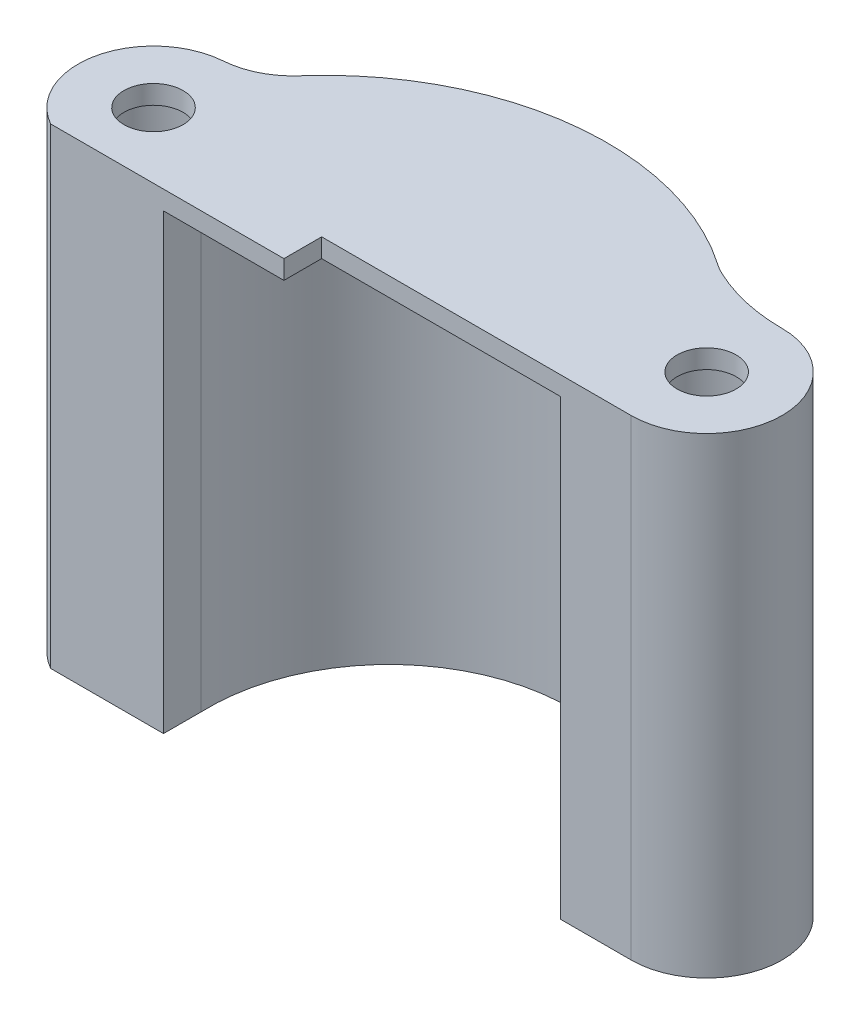
SolidWorks part; units mm, degrees
ref_plane "Front Plane" through (0, 0, 0) normal (0, 0, 1) x (1, 0, 0)
ref_plane "Top Plane" through (0, 0, 0) normal (0, 1, 0) x (1, 0, 0)
ref_plane "Right Plane" through (0, 0, 0) normal (1, 0, 0) x (0, 0, -1)
other "Bounding Box"
ref_plane "Default Plane" through (-8.9266, -12.7485, 0) normal (-0.1736, 0.9848, 0) x (0.9848, 0.1736, 0)
sketch "Sketch1" plane through (0, 0, 0) normal (0, 1, 0) x (1, 0, 0)
  line B0 (-13.6378, -15.7405) -> (-16.8128, -15.7405) construction
  line B1 (16.6091, -12.5655) -> (19.7841, -12.5655) construction
  arc B2 (-13.6378, -15.7405) -> (16.6091, -12.5655) centre (1.591, -15.1567) cw
  arc B3 (-16.8128, -15.7405) -> (19.7841, -12.5655) centre (1.6704, -16.283) cw
sketch_block_instance "Cover for wepon motor-1"
sketch_block "Cover for wepon motor" parameters "D3"=15.24, "D4"=18.4912, "D1"=3.175, "D2"=3.175
sketch "Sketch2" plane through (0, 0, 0) normal (0, 1, 0) x (1, 0, 0)
  line L0 (-13.6378, -18.9155) -> (-13.6378, -15.7405)
  line L1 (16.6091, -12.5655) -> (16.6091, -15.7405)
  line L2 (-23.1387, -18.9155) -> (-13.6378, -18.9155)
  line L3 (16.6091, -15.7405) -> (22.5457, -15.7405)
  arc A1 (-13.6378, -15.7405) -> (16.6091, -12.5655) centre (1.591, -15.1567) cw
  circle A2 centre (-19.9967, -13.3973) radius 4.7625
  circle A3 centre (22.5457, -9.3905) radius 4.7625
  arc A5 (-19.9967, -7.0473) -> (-23.1387, -18.9155) centre (-19.9967, -13.3973) ccw
  arc A7 (22.5457, -15.7405) -> (22.5457, -3.0405) centre (22.5457, -9.3905) ccw
  arc A8 (-19.9967, -7.0473) -> (-17.6403, -6.7838) centre (-19.9399, 3.1125) ccw
  arc A9 (22.5457, -3.0405) -> (15.4926, -1.3102) centre (22.5457, 12.1995) cw
  arc A20 (-17.6403, -6.7838) -> (15.4926, -1.3102) centre (1.663, -20.6134) cw
  dimension "D1" = 9.525
  dimension "D2" = 15.24
  dimension "D7" = 1.5875
  dimension "D9" = 1.5875
  dimension "D10" = 10.16
  dimension "D11" = 15.24
  dimension "D4" = 3.175
extrude "Boss-Extrude1" add sketch "Sketch2" along normal blind 38.1
sketch "Sketch3" plane through (0, 38.1, 0) normal (0, 1, 0) x (-1, 0, 0)
  line L0 (13.6378, 15.7405) -> (3.5038, 15.7405)
  line L1 (3.5038, 15.7405) -> (3.5038, 12.5655)
  line L2 (3.5038, 12.5655) -> (-16.6091, 12.5655)
  line L3 (13.6378, 18.9155) -> (13.6378, 15.7405)
  line L4 (-16.6091, 12.5655) -> (-16.6091, 15.7405)
  line L5 (-16.6091, 15.7405) -> (-22.5457, 15.7405)
  line L6 (13.6378, 18.9155) -> (13.6378, 15.7405)
  line L7 (-16.6091, 12.5655) -> (-16.6091, 15.7405)
  line L8 (-16.6091, 15.7405) -> (-22.5457, 15.7405)
  line L13 (23.1387, 18.9155) -> (13.6378, 18.9155)
  line L14 (23.1387, 18.9155) -> (13.6378, 18.9155)
  circle A0 centre (-22.5457, 9.3905) radius 2.4892
  circle A2 centre (19.9967, 13.3973) radius 2.4892
  arc A9 (-15.4926, 1.3102) -> (17.6403, 6.7838) centre (-1.663, 20.6134) ccw
  arc A10 (-15.4926, 1.3102) -> (17.6403, 6.7838) centre (-1.663, 20.6134) ccw
  arc A11 (19.9967, 7.0473) -> (17.6403, 6.7838) centre (19.9399, -3.1125) ccw
  arc A12 (19.9967, 7.0473) -> (23.1387, 18.9155) centre (19.9967, 13.3973) ccw
  arc A13 (-16.6091, 12.5655) -> (13.6378, 15.7405) centre (-1.591, 15.1567) ccw
  arc A14 (-22.5457, 15.7405) -> (-22.5457, 3.0405) centre (-22.5457, 9.3905) ccw
  arc A15 (-15.4926, 1.3102) -> (-22.5457, 3.0405) centre (-22.5457, -12.1995) ccw
  arc A20 (19.9967, 7.0473) -> (17.6403, 6.7838) centre (19.9399, -3.1125) ccw
  arc A21 (19.9967, 7.0473) -> (23.1387, 18.9155) centre (19.9967, 13.3973) ccw
  arc A23 (-22.5457, 15.7405) -> (-22.5457, 3.0405) centre (-22.5457, 9.3905) ccw
  arc A24 (-15.4926, 1.3102) -> (-22.5457, 3.0405) centre (-22.5457, -12.1995) ccw
  point P29 (2.8927, 12.5655)
  dimension "D3" = 4.9784
  dimension "D2" = 3.175
  dimension "D4" = 20.1129
  dimension "D1" = 0
extrude "Boss-Extrude2" add sketch "Sketch3" along normal blind 1.5875
sketch "Sketch4" plane through (0, 39.6875, 0) normal (0, 1, 0) x (-1, 0, 0)
  line L0 (3.5038, 15.7405) -> (3.5038, 12.5655) construction
  line L1 (13.6378, 15.7405) -> (3.5038, 15.7405)
  line L2 (13.6378, 15.7405) -> (13.6378, 18.9155)
  line L3 (13.6378, 18.9155) -> (3.5038, 18.9155)
  line L4 (3.5038, 15.7405) -> (3.5038, 18.9155)
  line L5 (23.1387, 18.9155) -> (13.6378, 18.9155) construction
  line L7 (3.5038, 12.5655) -> (-16.6091, 12.5655)
  line L8 (3.5038, 12.5655) -> (3.5038, 15.7405)
  line L9 (3.5038, 15.7405) -> (-16.6091, 15.7405)
  line L10 (-16.6091, 12.5655) -> (-16.6091, 15.7405)
  line M10 (13.6378, 18.9155) -> (13.6378, 15.7405)
  line M11 (13.6378, 15.7405) -> (3.5038, 15.7405)
  line M12 (3.5038, 15.7405) -> (3.5038, 12.5655)
  line M13 (3.5038, 12.5655) -> (-16.6091, 12.5655)
  line M14 (-16.6091, 12.5655) -> (-16.6091, 15.7405)
extrude "Boss-Extrude3" add sketch "Sketch4" against normal up to surface (1.5875 mm away) contours L9 M12 M14 M13 | L4 L3 M11 M10 up to face at (-1.3805, 38.1, 10.6147)
fillet "Fillet2" radius 6.35 2 edges at (15.4926, 19.8438, 1.3102) (-17.6403, 19.8438, 6.7838)
